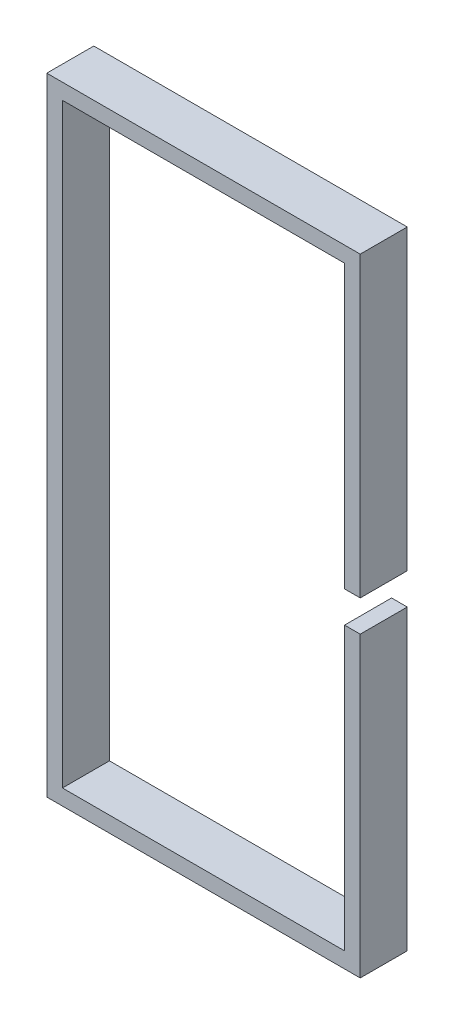
SolidWorks part; units mm, degrees
ref_plane "Front Plane" through (0, 0, 0) normal (0, 0, 1) x (1, 0, 0)
ref_plane "Top Plane" through (0, 0, 0) normal (0, 1, 0) x (1, 0, 0)
ref_plane "Right Plane" through (0, 0, 0) normal (1, 0, 0) x (0, 0, -1)
sketch "Sketch1" plane through (0, 0, 0) normal (0, 0, 1) x (1, 0, 0)
  line L0 (0, 0) -> (-200, 0)
  line L1 (-200, 0) -> (-200, -400)
  line L2 (-200, -400) -> (0, -400)
  line L3 (0, -400) -> (0, -210)
  line L4 (0, 0) -> (0, -190)
extrude "Extrude-Thin1" add sketch "Sketch1" along normal blind 30 thin thin type one direction wall 10
